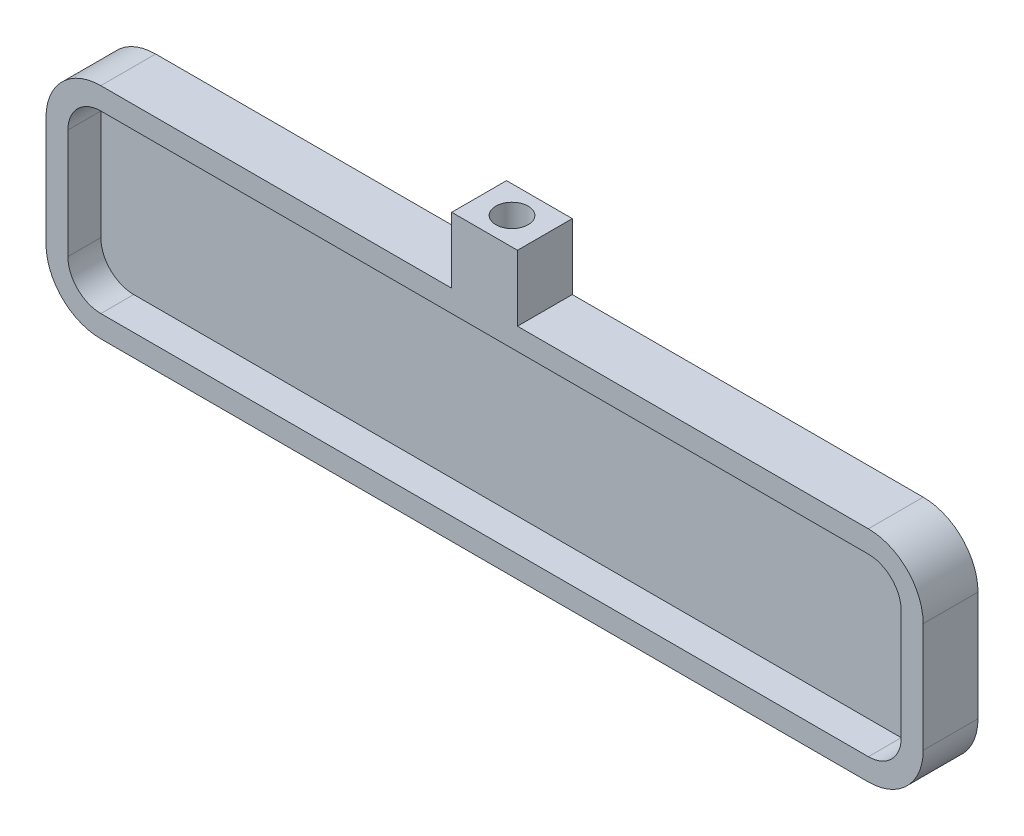
SolidWorks part; units mm, degrees
ref_plane "Front Plane" through (0, 0, 0) normal (0, 0, 1) x (1, 0, 0)
ref_plane "Top Plane" through (0, 0, 0) normal (0, 1, 0) x (1, 0, 0)
ref_plane "Right Plane" through (0, 0, 0) normal (1, 0, 0) x (0, 0, -1)
sketch "Sketch1" plane through (0, 0, 0) normal (0, 0, 1) x (1, 0, 0)
  line L1 (-40, -10) -> (40, -10)
  line L2 (-40, -10) -> (-40, 10)
  line L3 (-40, 10) -> (40, 10)
  line L4 (40, -10) -> (40, 10)
  line L5 (-40, -10) -> (40, 10) construction
  line L6 (-40, 10) -> (40, -10) construction
  point P0 (0, 0)
  dimension "D1" = 80
  dimension "D2" = 20
extrude "Boss-Extrude1" add sketch "Sketch1" along normal blind 5
fillet "Fillet1" radius 5 4 edges at (-40, 10, 2.5) (-40, -10, 2.5) (40, -10, 2.5) (40, 10, 2.5)
shell "Shell1" thickness 2
sketch "Sketch2" plane through (0, 10, 0) normal (0, 1, 0) x (1, 0, 0)
  line L0 (0, 0) -> (-3, 0)
  line L1 (35, 0) -> (-35, 0) construction
  line L2 (-3, 0) -> (-3, -5)
  line L3 (35, -5) -> (-35, -5) construction
  line L4 (-3, -5) -> (3, -5)
  line L5 (3, -5) -> (3, 0)
  line L6 (3, 0) -> (0, 0)
  dimension "D1" = 3
  dimension "D2" = 6
extrude "Boss-Extrude2" add sketch "Sketch2" along normal blind 6
sketch "Sketch3" plane through (0, 16, 0) normal (0, 1, 0) x (1, 0, 0)
  line L0 (-3, 0) -> (3, -5) construction
  circle A0 centre (0, -2.5) radius 1.475
  dimension "D1" = 2.95
extrude "Cut-Extrude1" cut sketch "Sketch3" against normal blind 4
